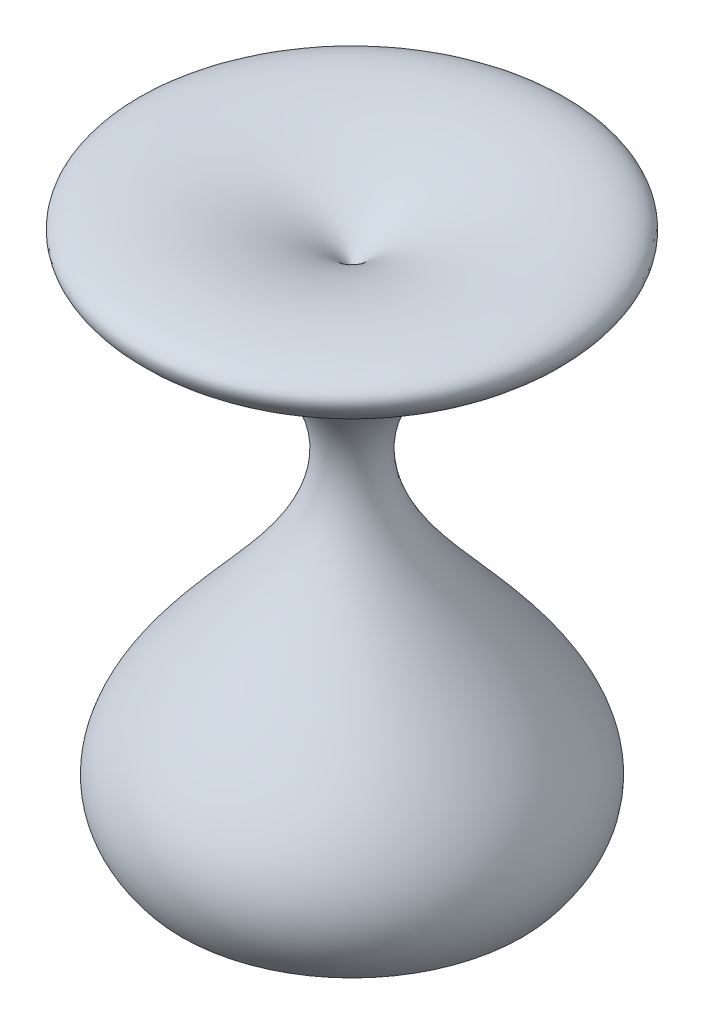
SolidWorks part; units mm, degrees
ref_plane "Front Plane" through (0, 0, 0) normal (0, 0, 1) x (1, 0, 0)
ref_plane "Top Plane" through (0, 0, 0) normal (0, 1, 0) x (1, 0, 0)
ref_plane "Right Plane" through (0, 0, 0) normal (1, 0, 0) x (0, 0, -1)
sketch "Sketch2" plane through (0, 0, 0) normal (0, 0, 1) x (1, 0, 0)
  line L0 (33.0078, 30.716) -> (33.0078, -34.1219) construction
  line L1 (21.1503, -32.1036) -> (33.0078, -32.1036)
  line L2 (33.0078, 19.8676) -> (33.0078, -32.1036)
  spline S0 degree 3 poles (21.1503, 17.2186) (50.5819, -2.2559) (-4.1062, -15.6866) (21.1503, -32.1036) knots 0 0 0 0 1 1 1 1
  spline S1 degree 3 poles (21.1503, 17.2186) (-3.2159, 27.2899) (27.7842, 28.0273) (33.0078, 19.8676) knots 0 0 0 0 1 1 1 1
revolve "Revolve1" add sketch "Sketch2" angle 360 about L0
sketch "Sketch3" plane through (0, -32.1036, 0) normal (0, -1, 0) x (-1, 0, 0)
  circle A2 centre (-33.0078, 0) radius 16.5968
extrude "Cut-Extrude1" cut sketch "Sketch3" against normal blind 5
